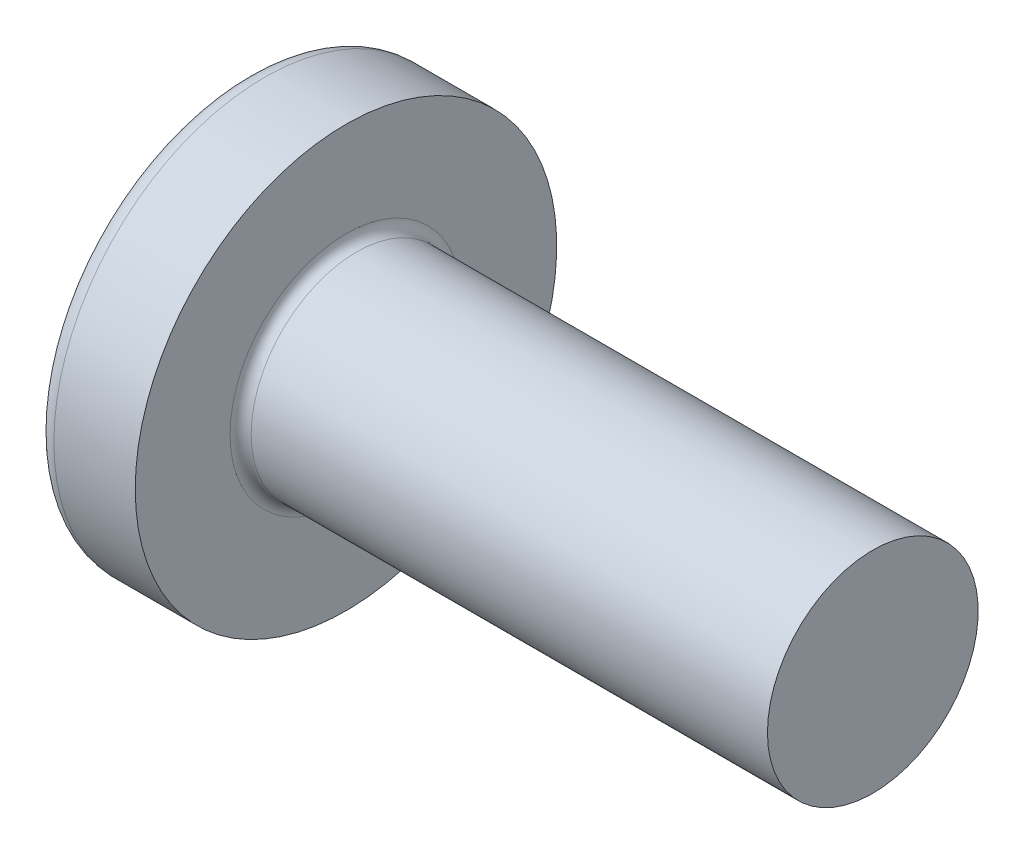
SolidWorks part; units mm, degrees
material "普通碳钢"
ref_plane "Plane1" through (0, 0, 0) normal (0, 0, 1) x (1, 0, 0)
ref_plane "Plane2" through (0, 0, 0) normal (0, 1, 0) x (1, 0, 0)
ref_plane "Plane3" through (0, 0, 0) normal (1, 0, 0) x (0, 0, -1)
sketch "BodySke" plane through (0, 0, 0) normal (0, 0, 1) x (1, 0, 0)
  line L0 (3.1, 2) -> (3.1, 4)
  line L1 (3.45, 6.35) -> (3.45, -3.175) construction
  line L2 (-25.4, 0) -> (127, 0) construction
  line L3 (13.1, 0) -> (0, 0)
  line L4 (3.1, 2) -> (13.1, 2)
  line L5 (13.1, 2) -> (13.1, 0)
  line L6 (1.5553, 4) -> (3.1, 4)
  line L8 (7.1, 6.35) -> (7.1, -3.175) construction
  arc A0 (1.2654, 3.8534) -> (0, 0) centre (6.5, 0) ccw
  arc A2 (1.2654, 3.8534) -> (1.5553, 4) centre (1.5553, 3.64) cw
  dimension "Head_crown_rad" = 6.5
  dimension "Head_fillet_rad" = 0.36
  dimension "Length" = 10
  dimension "Head_ht" = 3.1
  dimension "Head_dia" = 8
  dimension "Advance" = 0.7
  dimension "Thread_nom" = 6
  dimension "Diameter" = 4
revolve "Base-Revolve" add sketch "BodySke"
cosmetic thread "ThreadCosmetic" [suppressed]
fillet "Fillet1" radius 0.2 1 edges at (3.1, 0, 2)
sketch "Sketch3" plane through (0, 0, 0) normal (1, 0, 0) x (0, 0, -1)
  line L0 (0.515, -2.15) -> (-0.515, -2.15)
  line L1 (0.515, -2.15) -> (0.515, 2.15)
  line L2 (-0.515, 2.15) -> (0.515, 2.15)
  line L3 (-0.515, 2.15) -> (-0.515, -2.15)
  dimension "Cross_dia" = 4.3
  dimension "D1" = 2.15
  dimension "Cross_width" = 1.03
  dimension "D2" = 0.515
ref_plane "Plane4" through (2.34, 0, 0) normal (1, 0, 0) x (0, 0, -1)
sketch "Sketch4" plane through (2.34, 0, 0) normal (1, 0, 0) x (0, 0, -1)
  line L0 (0.515, -0.9833) -> (-0.515, -0.9833)
  line L1 (0.515, -0.9833) -> (0.515, 0.9833)
  line L2 (-0.515, 0.9833) -> (0.515, 0.9833)
  line L3 (-0.515, 0.9833) -> (-0.515, -0.9833)
  dimension "D1" = 1.03
  dimension "D2" = 1.9666
  dimension "D3" = 0.515
  dimension "D4" = 0.9833
loft "Recess" cut profiles "Sketch3", "Sketch4"
pattern_circular "RecPat" count 2 every 90 about axis through (0, 0, 0) along (1, 0, 0) of "Recess"
sketch "RecCorSke" plane through (0, 0, 0) normal (0, 0, 1) x (1, 0, 0)
  line L0 (-3.175, 0) -> (15.875, 0) construction
  line L1 (-25.4, 0) -> (127, 0) construction
  line L2 (0, 0) -> (0, 1.0146)
  line L3 (0, 1.0146) -> (2.34, 0.851)
  line L4 (2.34, 0.851) -> (2.6165, 0)
  line L5 (2.6165, 0) -> (0, 0)
  dimension "Diameter" = 1.702
  dimension "Depth" = 2.34
  dimension "Draft_angle" = 4
  dimension "Bottom_angle" = 18
revolve "RecessCore" cut sketch "RecCorSke" angle 360 about L0
sketch "ThdSchSke" plane through (0, 0, 0) normal (0, 0, 1) x (1, 0, 0)
  line L0 (7.1, -1.61) -> (6.8269, -2)
  line L1 (7.1, -1.61) -> (7.3731, -2)
  line L2 (7.3731, -2) -> (7.3731, -2.5)
  line L3 (-3.175, 0) -> (5.1513, 0) construction
  line L5 (7.3731, -2.5) -> (6.8269, -2.5)
  line L6 (6.8269, -2.5) -> (6.8269, -2)
  dimension "Diameter" = 4
  dimension "SideAngle" = 55
  dimension "VeeAngle" = 70
  dimension "Thread_minor" = 3.22
  dimension "Overcut" = 5
  dimension "Start" = 7.1
revolve "ThreadSchematic" [suppressed] cut sketch "ThdSchSke" angle 360 about L3
pattern_linear "ThdSchPat" [suppressed]
sketch "草图1" plane through (13.1, 0, 0) normal (1, 0, 0) x (0, 0, -1)
  circle A0 centre (0, 0) radius 2 construction
  circle A1 centre (0, 0) radius 2
equation "\"D1@Sketch3\" = \"Cross_dia@Sketch3\" / 2"
equation "\"D2@Sketch3\" = \"Cross_width@Sketch3\" / 2"
equation "\"Depth@RecCorSke\" = \"Cross_depth@Plane4\""
equation "\"D1@Sketch4\" = \"Cross_width@Sketch3\""
equation "\"D2@Sketch4\" = \"Cross_dia@Sketch3\" - 2.0 * \"Cross_depth@Plane4\" * tan(26.5  * 0.017453292)"
equation "\"D3@Sketch4\" = \"D1@Sketch4\" / 2"
equation "\"D4@Sketch4\" = \"D2@Sketch4\" / 2"
equation "\"Thread_length@ThreadCosmetic\" = ((sgn( (\"Length@BodySke\" - \"Advance@BodySke\" * 2.0 ) - \"Thread_nom@BodySke\" )-1)*( (\"Length@BodySke\" - \"Advance@BodySke\" * 2.0 ) - \"Thread_nom@BodySke\" ))/-2+ \"Thread_nom@BodySke\""
equation "\"Thread_minor@ThdSchSke\" = \"Thread_minor@ThreadCosmetic\""
equation "\"Diameter@ThdSchSke\" = \"Diameter@BodySke\""
equation "\"Overcut@ThdSchSke\" = \"Diameter@BodySke\" * 1.25"
equation "\"Start@ThdSchSke\" = \"Head_ht@BodySke\" + \"Length@BodySke\" - \"Thread_length@ThreadCosmetic\"  '---Non-countersunk---"
equation "\"Num_threads@ThdSchPat\" = int( \"Thread_length@ThreadCosmetic\" / \"Advance@BodySke\" + 0.999 )  + 1"
equation "\"Advance@ThdSchPat\" = \"Thread_length@ThreadCosmetic\" /  (\"Num_threads@ThdSchPat\" - 1) 'relax it"
